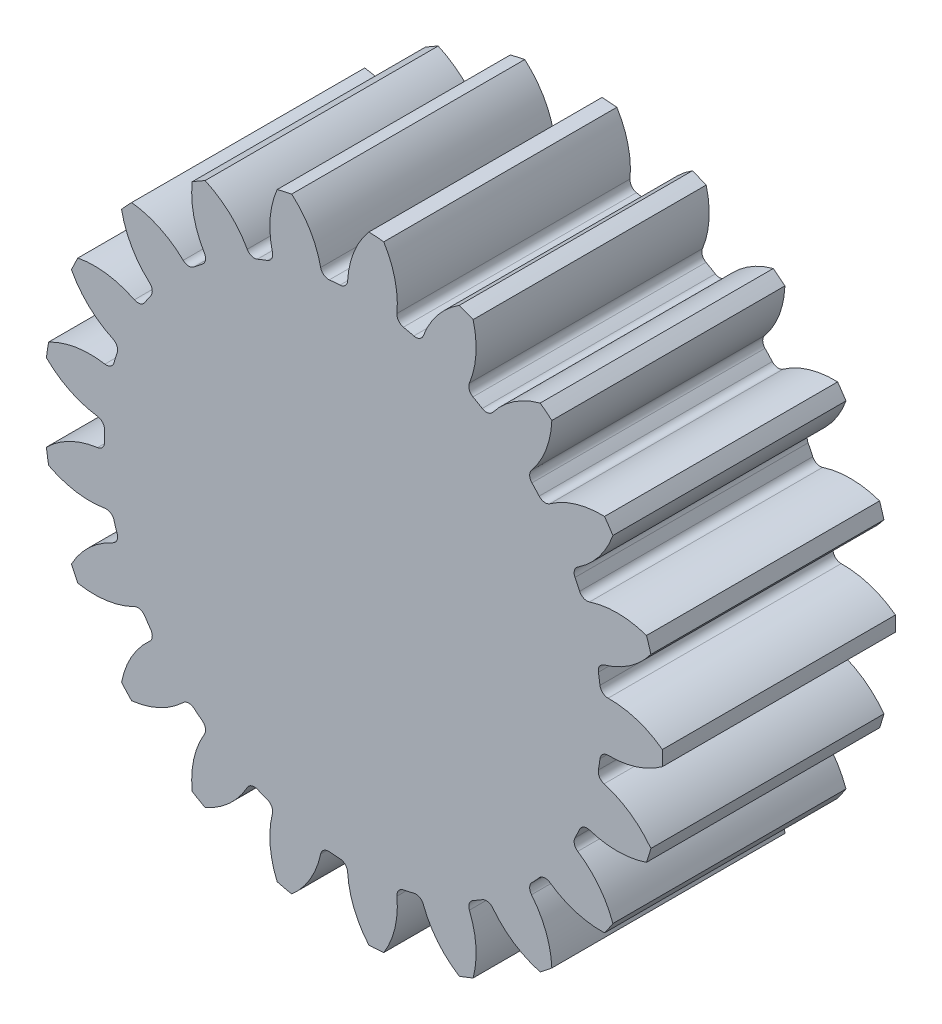
SolidWorks part; units mm, degrees
ref_plane "Front Plane" through (0, 0, 0) normal (0, 0, 1) x (1, 0, 0)
ref_plane "Top Plane" through (0, 0, 0) normal (0, 1, 0) x (1, 0, 0)
ref_plane "Right Plane" through (0, 0, 0) normal (1, 0, 0) x (0, 0, -1)
sketch "Sketch1" plane through (0, 0, 0) normal (0, 0, 1) x (1, 0, 0)
  circle A0 centre (0, 0) radius 31.5
  circle A1 centre (0, 0) radius 34.5
  circle A2 centre (0, 0) radius 27.75
  dimension "D1" = 63
  dimension "D2" = 69
  dimension "D3" = 6.75
extrude "Boss-Extrude1" add sketch "Sketch1" along normal mid plane 26 contours A1
sketch "Sketch4" plane through (0, 0, 0) normal (0, 0, 1) x (1, 0, 0)
  line L0 (0, 0) -> (-34.5, 0) construction
  line L1 (-31.4119, -2.354) -> (-31.4119, 2.354) construction
  line L2 (0, 0) -> (-27.713, -1.4331) construction
  line L3 (-26.3638, 0) -> (-35.257, -4.147) construction
  line L4 (0, 0) -> (-34.1147, 5.142) construction
  line L5 (-31.4119, 2.354) -> (-30.7102, 7.0094) construction
  circle A0 centre (0, 0) radius 34.5 construction
  arc A1 (-35.1006, -5.3105) -> (-27.713, -1.4331) centre (-27.198, -11.3907) cw
  arc A2 (-35.1006, 5.3105) -> (-27.713, 1.4331) centre (-27.198, 11.3907) ccw
  arc A3 (-35.1006, 5.3105) -> (-35.1006, -5.3105) centre (0, 0) ccw
  circle A4 centre (0, 0) radius 27.75
  arc A5 (-27.713, 1.4331) -> (-27.713, -1.4331) centre (0, 0) ccw
  circle A6 centre (0, 0) radius 34.5
  arc A7 (-34.2284, -4.3202) -> (-34.2284, 4.3202) centre (0, 0) ccw
  circle A10 centre (0, 0) radius 35.5 construction
  circle A11 centre (0, 0) radius 34.5 construction
  circle A15 centre (0, 0) radius 31.5
  circle A16 centre (0, 0) radius 31.5
  point P20 (32.9925, 10.0868)
  point P22 (35.5, 0)
  dimension "D4" = 25
  dimension "D5" = 8.571
  dimension "D1" = 0
  dimension "D2" = 0
  dimension "D3" = 1
  dimension "D6" = 0
extrude "Cut-Extrude1" cut sketch "Sketch4" against normal through all both and the other way through all contours A16 A2 A3 A1 | A2 A16 A1 A5
fillet "Fillet1" radius 0.9 2 edges at (-27.713, -1.4331, 0) (-27.713, 1.4331, 0)
pattern_circular "CirPattern1" count 21 over 360 about axis through (0, 0, 0) along (0, 0, 1) of "Cut-Extrude1", "Fillet1"
equation "\"Module\"= 3mm"
equation "\"Number of Teeth\" = 21"
equation "\"D1@Sketch1\"=\"Module\" * \"Number of Teeth\""
equation "\"D2@Sketch1\"=(\"Number of Teeth\" + 2) * \"Module\""
equation "\"D3@Sketch1\"=\"Module\" * if(\"Module\"=>1.25,2.25,2.4)"
equation "\"D5@Sketch4\"=180 / \"Number of Teeth\""
equation "\"D1@Fillet1\"=.3 * \"Module\""
equation "\"D1@CirPattern1\"=\"Number of Teeth\""
